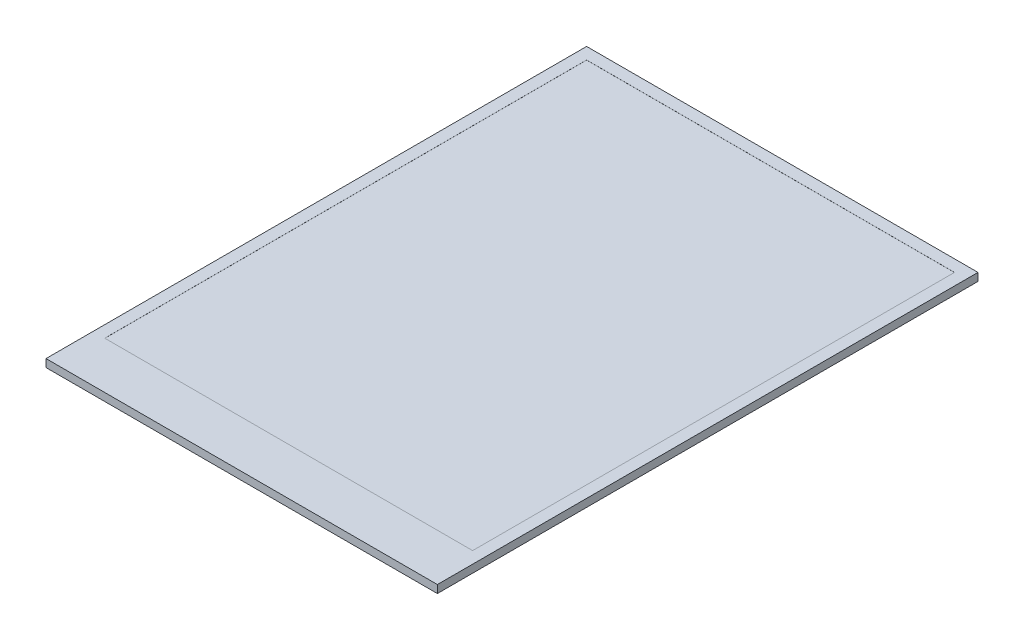
SolidWorks part; units mm, degrees
ref_plane "Front Plane" through (0, 0, 0) normal (0, 0, 1) x (1, 0, 0)
ref_plane "Top Plane" through (0, 0, 0) normal (0, 1, 0) x (1, 0, 0)
ref_plane "Right Plane" through (0, 0, 0) normal (1, 0, 0) x (0, 0, -1)
sketch "Sketch1" plane through (0, 0, 0) normal (0, 1, 0) x (1, 0, 0)
  line L1 (0, 0) -> (49.96, 0)
  line L2 (0, 0) -> (0, -69.01)
  line L3 (0, -69.01) -> (49.96, -69.01)
  line L4 (49.96, 0) -> (49.96, -69.01)
  dimension "D1" = 49.96
  dimension "D2" = 69.01
extrude "Boss-Extrude1" add sketch "Sketch1" along normal blind 1
sketch "Sketch2" plane through (0, 1, 0) normal (0, 1, 0) x (1, 0, 0)
  line L0 (0, 0) -> (0, -69.01) construction
  line L1 (1.5, -1.5) -> (48.46, -1.5)
  line L2 (1.5, -1.5) -> (1.5, -63.01)
  line L3 (1.5, -63.01) -> (48.46, -63.01)
  line L4 (48.46, -1.5) -> (48.46, -63.01)
  line L5 (49.96, 0) -> (0, 0) construction
  line L6 (49.96, -69.01) -> (49.96, 0) construction
  line L7 (0, -69.01) -> (49.96, -69.01) construction
  dimension "D1" = 1.5
  dimension "D2" = 1.5
  dimension "D3" = 1.5
  dimension "D4" = 6
extrude "Cut-Extrude1" cut sketch "Sketch2" against normal blind 0.01
equation "\"D2@Sketch2\"=\"D1@Sketch2\""
equation "\"D3@Sketch2\"=\"D2@Sketch2\""
equation "\"D4@Sketch2\"=6mm"
